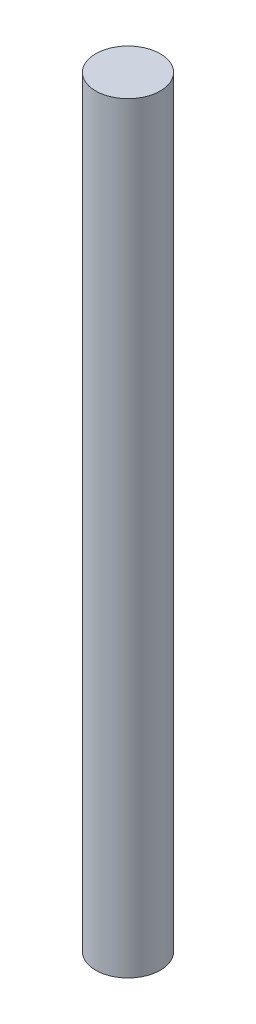
SolidWorks part; units mm, degrees
ref_plane "Front Plane" through (0, 0, 0) normal (0, 0, 1) x (1, 0, 0)
ref_plane "Top Plane" through (0, 0, 0) normal (0, 1, 0) x (1, 0, 0)
ref_plane "Right Plane" through (0, 0, 0) normal (1, 0, 0) x (0, 0, -1)
sketch "Sketch1" plane through (0, 0, 0) normal (0, 1, 0) x (1, 0, 0)
  circle A0 centre (0, 0) radius 2.5
  dimension "D1" = 5
extrude "Boss-Extrude1" add sketch "Sketch1" along normal blind 37 and the other way blind 22
